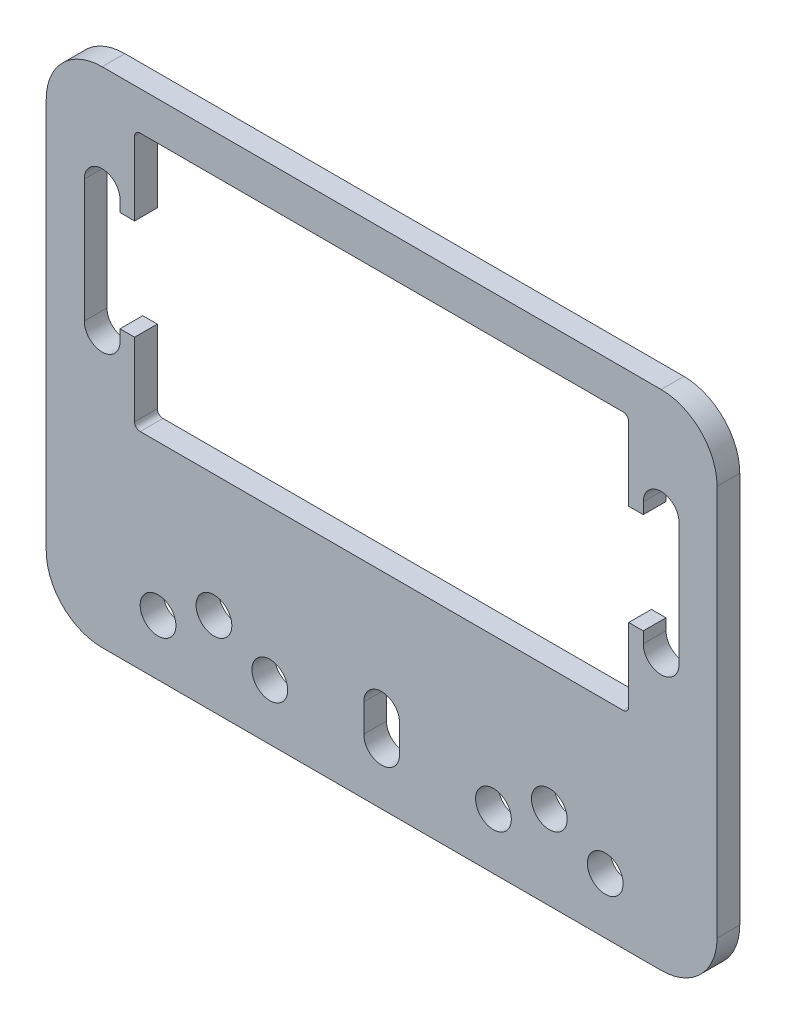
SolidWorks part; units mm, degrees
ref_plane "Front Plane" through (0, 0, 0) normal (0, 0, 1) x (1, 0, 0)
ref_plane "Top Plane" through (0, 0, 0) normal (0, 1, 0) x (1, 0, 0)
ref_plane "Right Plane" through (0, 0, 0) normal (1, 0, 0) x (0, 0, -1)
sketch "Sketch1" plane through (0, 0, 0) normal (0, 0, 1) x (1, 0, 0)
  line L1 (-30, -22.5) -> (30, -22.5)
  line L2 (-30, -22.5) -> (-30, 22.5)
  line L3 (-30, 22.5) -> (30, 22.5)
  line L4 (30, -22.5) -> (30, 22.5)
  line L5 (-30, -22.5) -> (30, 22.5) construction
  line L6 (-30, 22.5) -> (30, -22.5) construction
  point P0 (0, 0)
  dimension "D1" = 60
  dimension "D2" = 45
extrude "Boss-Extrude1" add sketch "Sketch1" along normal blind 2.032
fillet "Fillet1" radius 5 4 edges at (-30, -22.5, 1.016) (30, -22.5, 1.016) (-30, 22.5, 1.016) (30, 22.5, 1.016)
sketch "Sketch2" plane through (0, 0, 2.032) normal (0, 0, 1) x (1, 0, 0)
  line L0 (-41.2577, -7.5) -> (43.7202, -7.5) construction
  line L1 (-25, -22.5) -> (25, -22.5) construction
  line L2 (0, -54.6431) -> (0, 54.6431) construction
  line L3 (-22.098, -4.057) -> (22.098, -4.057)
  line L4 (-22.098, -4.057) -> (-22.098, 19.057)
  line L5 (-22.098, 19.057) -> (22.098, 19.057)
  line L6 (22.098, -4.057) -> (22.098, 19.057)
  line L7 (-22.098, -4.057) -> (22.098, 19.057) construction
  line L8 (-22.098, 19.057) -> (22.098, -4.057) construction
  line L9 (-33.3183, 7.5) -> (35.3128, 7.5) construction
  line L10 (25, 22.5) -> (-25, 22.5) construction
  point P4 (0, 7.5)
  dimension "D1" = 15
  dimension "D2" = 23.114
  dimension "D3" = 44.196
extrude "Cut-Extrude1" cut sketch "Sketch2" against normal through all
fillet "Fillet2" radius 0.5 4 edges at (22.098, 19.057, 1.016) (22.098, -4.057, 1.016) (-22.098, -4.057, 1.016) (-22.098, 19.057, 1.016)
sketch "Sketch3" plane through (0, 0, 2.032) normal (0, 0, 1) x (1, 0, 0)
  line L0 (-25, 3) -> (-25, 2) construction
  line L1 (-23.4, 3) -> (-23.4, 2)
  line L2 (-26.6, 3) -> (-26.6, 2)
  line L3 (-22.098, 7.5) -> (22.098, 7.5) construction
  line L4 (-22.098, 18.557) -> (-22.098, -3.557) construction
  line L5 (22.098, -3.557) -> (22.098, 18.557) construction
  line L6 (0, 18.6557) -> (0, -3.4503) construction
  line L7 (0, -54.6431) -> (0, 54.6431) construction
  line L8 (-25, 12) -> (-25, 13) construction
  line L9 (-23.4, 12) -> (-23.4, 13)
  line L10 (-26.6, 12) -> (-26.6, 13)
  line L11 (25, 3) -> (25, 2) construction
  line L12 (23.4, 3) -> (23.4, 2)
  line L13 (26.6, 3) -> (26.6, 2)
  line L14 (25, 12) -> (25, 13) construction
  line L15 (23.4, 12) -> (23.4, 13)
  line L16 (26.6, 12) -> (26.6, 13)
  line L17 (26.6, 12) -> (26.6, 3)
  line L18 (23.4, 12) -> (20.8421, 12)
  line L23 (23.4, 3) -> (20.8421, 3)
  line L24 (20.8421, 12) -> (20.8421, 3)
  line L25 (-26.6, 3) -> (-26.6, 12)
  line L26 (-23.4, 12) -> (-21.0378, 12)
  line L27 (-23.4, 3) -> (-21.0378, 3)
  line L28 (-21.0378, 12) -> (-21.0378, 3)
  arc A0 (-23.4, 3) -> (-26.6, 3) centre (-25, 3) ccw
  arc A1 (-26.6, 2) -> (-23.4, 2) centre (-25, 2) ccw
  arc A2 (-23.4, 12) -> (-26.6, 12) centre (-25, 12) cw
  arc A3 (-26.6, 13) -> (-23.4, 13) centre (-25, 13) cw
  arc A4 (23.4, 3) -> (26.6, 3) centre (25, 3) cw
  arc A5 (26.6, 2) -> (23.4, 2) centre (25, 2) cw
  arc A6 (23.4, 12) -> (26.6, 12) centre (25, 12) ccw
  arc A7 (26.6, 13) -> (23.4, 13) centre (25, 13) ccw
  point P2 (-25, 2.5)
  point P20 (-25, 12.5)
  point P27 (25, 2.5)
  point P34 (25, 12.5)
  line M7 (-22.098, -3.557) -> (-22.098, 18.557)
  dimension "D1" = 10
  dimension "D2" = 50
  dimension "D3" = 3.2
  dimension "D4" = 1
extrude "Cut-Extrude2" cut sketch "Sketch3" against normal through all contours A3 L10 A2 L9 | L26 A2 L25 A0 L27 M7 | L2 A1 L1 A0 | A5 L13 A4 L12 | A6 L18 L24 L23 A4 L17 | L16 A7 L15 A6
sketch "Sketch4" plane through (0, 0, 2.032) normal (0, 0, 1) x (1, 0, 0)
  line L0 (0, -54.6431) -> (0, 54.6431) construction
  line L1 (-30, -15) -> (30, -15) construction
  line L2 (-30, 17.5) -> (-30, -17.5) construction
  line L3 (30, -17.5) -> (30, 17.5) construction
  line L4 (-25, -22.5) -> (25, -22.5) construction
  line L5 (0, 0) -> (0, -6.6395) construction
  line L6 (-30, -17.5) -> (30, -17.5) construction
  line L7 (0, -15) -> (0, -17.5) construction
  line L8 (1.6, -15) -> (1.6, -17.5)
  line L9 (-1.6, -15) -> (-1.6, -17.5)
  circle A0 centre (-15, -15) radius 1.6
  circle A1 centre (0, -15) radius 1.6 construction
  circle A2 centre (15, -15) radius 1.6
  circle A3 centre (-22.5, -15) radius 1.6 construction
  circle A4 centre (-7.5, -15) radius 1.6 construction
  circle A5 centre (7.5, -15) radius 1.6 construction
  circle A6 centre (22.5, -15) radius 1.6 construction
  circle A7 centre (0, -17.5) radius 1.6 construction
  circle A8 centre (10, -17.5) radius 1.6
  circle A9 centre (-10, -17.5) radius 1.6
  circle A10 centre (20, -17.5) radius 1.6
  circle A11 centre (-20, -17.5) radius 1.6
  arc A12 (1.6, -15) -> (-1.6, -15) centre (0, -15) ccw
  arc A13 (-1.6, -17.5) -> (1.6, -17.5) centre (0, -17.5) ccw
  point P39 (0, -16.25)
  dimension "D1" = 3.2
  dimension "D2" = 7.5
  dimension "D3" = 15
  dimension "D4" = 15
  dimension "D5" = 15
  dimension "D6" = 7.5
  dimension "D7" = 5
  dimension "D8" = 10
  dimension "D9" = 10
  dimension "D10" = 10
extrude "Cut-Extrude3" cut sketch "Sketch4" against normal through all
sketch "Alignment_Sketch" plane through (0, 0, 0) normal (0, 0, -1) x (-1, 0, 0)
  line L0 (-15, -15) -> (15, -15) construction
  point P0 (-15, -15)
  point P1 (15, -15)
